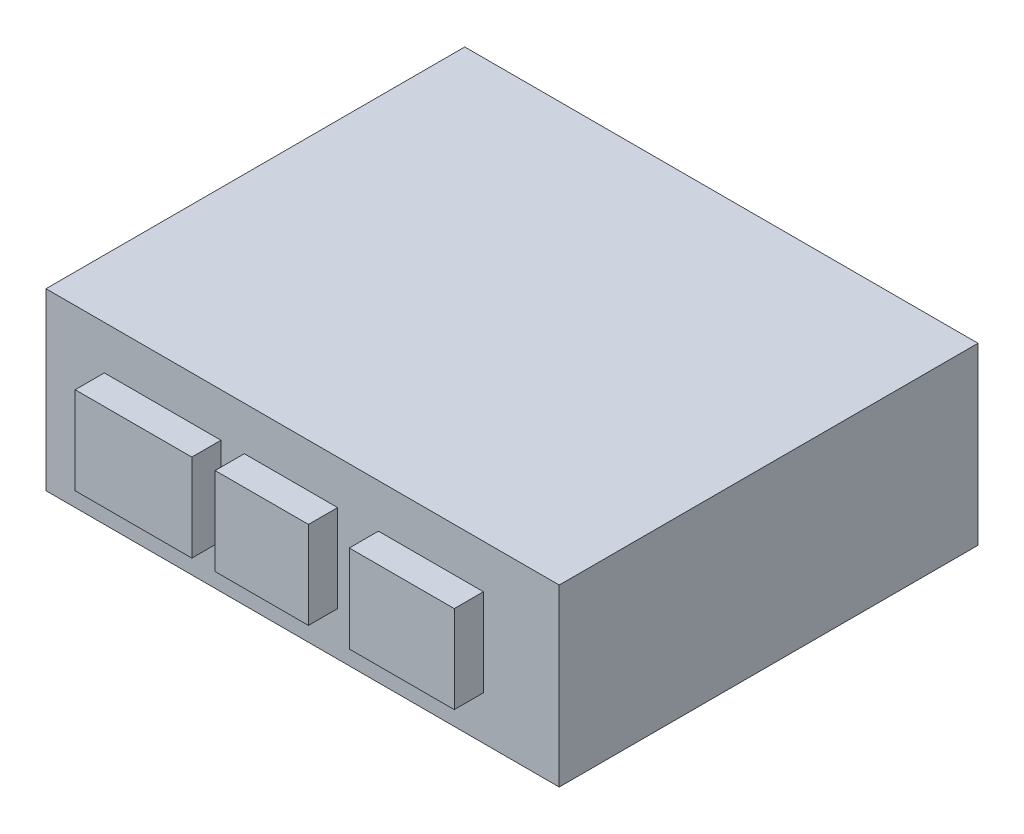
SolidWorks part; units mm, degrees
ref_plane "Front Plane" through (0, 0, 0) normal (0, 0, 1) x (1, 0, 0)
ref_plane "Top Plane" through (0, 0, 0) normal (0, 1, 0) x (1, 0, 0)
ref_plane "Right Plane" through (0, 0, 0) normal (1, 0, 0) x (0, 0, -1)
sketch "Sketch1" plane through (0, 0, 0) normal (0, 1, 0) x (1, 0, 0)
  line L1 (-44, -35.9) -> (44, -35.9)
  line L2 (-44, -35.9) -> (-44, 35.9)
  line L3 (-44, 35.9) -> (44, 35.9)
  line L4 (44, -35.9) -> (44, 35.9)
  line L5 (-44, -35.9) -> (44, 35.9) construction
  line L6 (-44, 35.9) -> (44, -35.9) construction
  point P0 (0, 0)
  dimension "D1" = 88
  dimension "D2" = 71.8
extrude "Boss-Extrude1" add sketch "Sketch1" along normal blind 30
sketch "Sketch2" plane through (0, 0, 35.9) normal (0, 0, 1) x (1, 0, 0)
  line L0 (-44, 30) -> (-44, 0) construction
  line L1 (-34, 7.5) -> (-14, 7.5)
  line L2 (-34, 7.5) -> (-34, 22.5)
  line L3 (-34, 22.5) -> (-14, 22.5)
  line L4 (-14, 7.5) -> (-14, 22.5)
  line L5 (-34, 7.5) -> (-14, 22.5) construction
  line L6 (-34, 22.5) -> (-14, 7.5) construction
  line L7 (-10, 7.5) -> (6, 7.5)
  line L8 (-10, 7.5) -> (-10, 22.5)
  line L9 (-10, 22.5) -> (6, 22.5)
  line L10 (6, 7.5) -> (6, 22.5)
  line L11 (-10, 7.5) -> (6, 22.5) construction
  line L12 (-10, 22.5) -> (6, 7.5) construction
  line L13 (13, 7.5) -> (31, 7.5)
  line L14 (13, 7.5) -> (13, 22.5)
  line L15 (13, 22.5) -> (31, 22.5)
  line L16 (31, 7.5) -> (31, 22.5)
  line L17 (13, 7.5) -> (31, 22.5) construction
  line L18 (13, 22.5) -> (31, 7.5) construction
  line L19 (-44, 30) -> (44, 30) construction
  point P0 (-24, 15)
  point P5 (-2, 15)
  point P10 (22, 15)
  dimension "D1" = 10
  dimension "D2" = 30
  dimension "D3" = 57
  dimension "D4" = 34
  dimension "D5" = 50
  dimension "D6" = 75
  dimension "D7" = 15
  dimension "D8" = 15
  dimension "D9" = 15
  dimension "D10" = 15
extrude "Boss-Extrude2" add sketch "Sketch2" along normal blind 5
